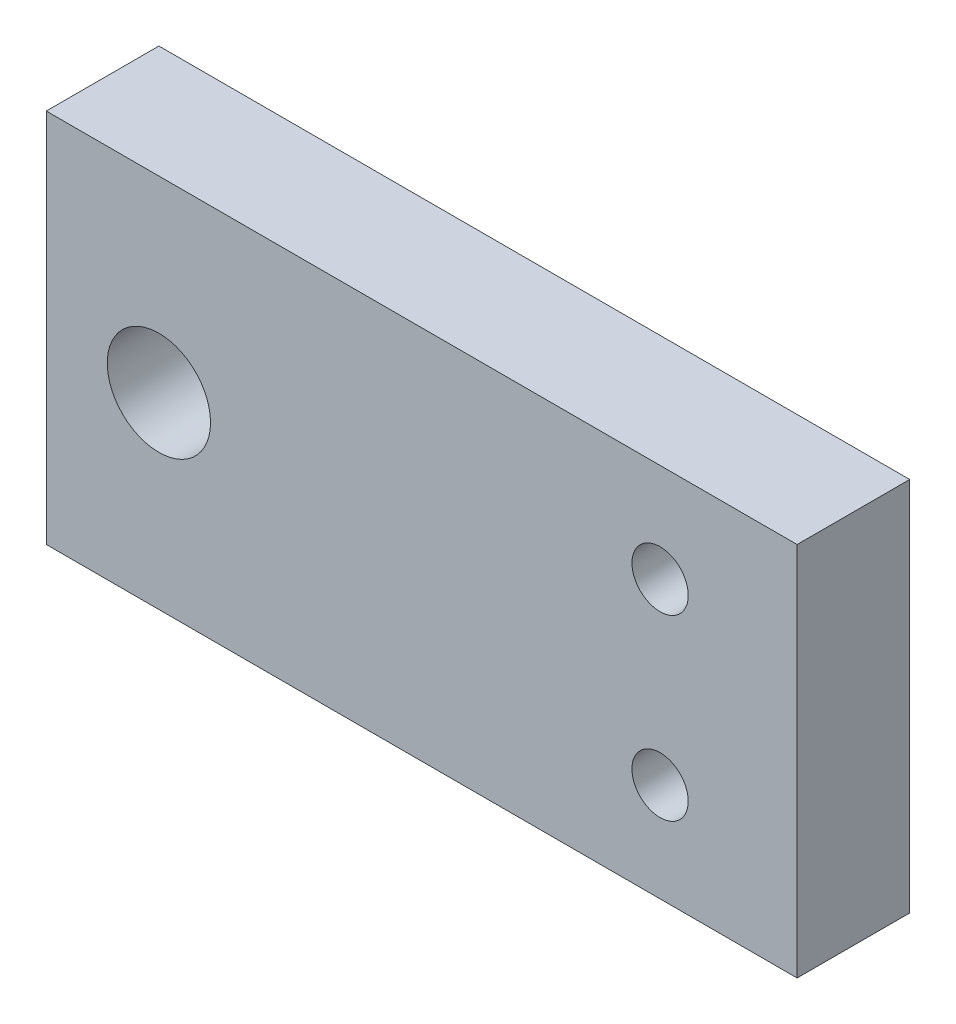
SolidWorks part; units mm, degrees
ref_plane "Alzado" through (0, 0, 0) normal (0, 0, 1) x (1, 0, 0)
ref_plane "Planta" through (0, 0, 0) normal (0, 1, 0) x (1, 0, 0)
ref_plane "Vista lateral" through (0, 0, 0) normal (1, 0, 0) x (0, 0, -1)
sketch "Croquis1" plane through (0, 0, 0) normal (0, 0, 1) x (1, 0, 0)
  line L0 (-7.8878, 0) -> (82.2791, 0) construction
  line L1 (0, 10) -> (40, 10)
  line L2 (0, 10) -> (0, -10)
  line L3 (0, -10) -> (40, -10)
  line L4 (40, 10) -> (40, -10)
  dimension "D1" = 20
  dimension "D2" = 40
extrude "Saliente-Extruir1" add sketch "Croquis1" along normal blind 6
sketch "Croquis2" plane through (0, 0, 0) normal (0, 0, -1) x (-1, 0, 0)
  line L1 (-29, 2.25) -> (-11, 2.25)
  line L2 (-29, 2.25) -> (-29, -2.25)
  line L3 (-29, -2.25) -> (-11, -2.25)
  line L4 (-11, 2.25) -> (-11, -2.25)
  line L5 (-40, -10) -> (-40, 10) construction
  line L6 (4.002, 0) -> (-76.2926, 0) construction
  dimension "D1" = 4.5
  dimension "D2" = 18
  dimension "D3" = 11
extrude "Saliente-Extruir2" add sketch "Croquis2" along normal blind 1.5
sketch "Croquis3" plane through (0, 0, 6) normal (0, 0, 1) x (1, 0, 0)
  line L0 (0, 10) -> (0, -10) construction
  circle A0 centre (6, 0) radius 2.75
  dimension "D2" = 5.5
  dimension "D1" = 6
extrude "Cortar-Extruir1" cut sketch "Croquis3" against normal through all
sketch "Croquis4" plane through (0, 0, 6) normal (0, 0, 1) x (1, 0, 0)
  circle A0 centre (32.7, 4.75) radius 1.5
  circle A1 centre (32.7, -4.75) radius 1.5
  dimension "D1" = 3
extrude "Cortar-Extruir2" cut sketch "Croquis4" against normal through all
sketch "Croquis5" plane through (0, 0, 0) normal (0, 0, -1) x (-1, 0, 0)
  line L1 (-29.5246, 4.75) -> (-31.1123, 7.5)
  line L2 (-31.1123, 7.5) -> (-34.2877, 7.5)
  line L3 (-34.2877, 7.5) -> (-35.8754, 4.75)
  line L4 (-35.8754, 4.75) -> (-34.2877, 2)
  line L5 (-34.2877, 2) -> (-31.1123, 2)
  line L6 (-31.1123, 2) -> (-29.5246, 4.75)
  line L7 (-29.5246, -4.75) -> (-31.1123, -2)
  line L8 (-31.1123, -2) -> (-34.2877, -2)
  line L9 (-34.2877, -2) -> (-35.8754, -4.75)
  line L10 (-35.8754, -4.75) -> (-34.2877, -7.5)
  line L11 (-34.2877, -7.5) -> (-31.1123, -7.5)
  line L12 (-31.1123, -7.5) -> (-29.5246, -4.75)
  circle A0 centre (-32.7, 4.75) radius 2.75 construction
  circle A1 centre (-32.7, -4.75) radius 2.75 construction
  dimension "D1" = 5.5
extrude "Cortar-Extruir3" cut sketch "Croquis5" against normal blind 2
